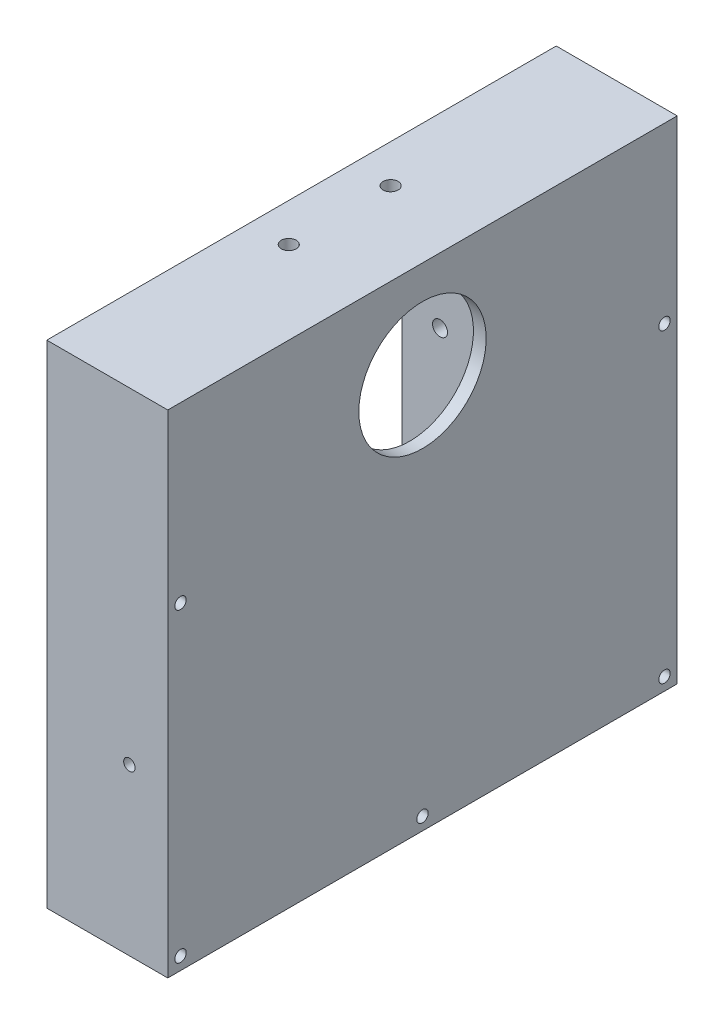
SolidWorks part; units mm, degrees
ref_plane "정면" through (0, 0, 0) normal (0, 0, 1) x (1, 0, 0)
ref_plane "윗면" through (0, 0, 0) normal (0, 1, 0) x (1, 0, 0)
ref_plane "우측면" through (0, 0, 0) normal (1, 0, 0) x (0, 0, -1)
ref_plane "평면1" through (0, 0, 0) normal (-1, 0, 0) x (0, -1, 0)
sketch "스케치1" plane through (0, 0, 0) normal (-1, 0, 0) x (0, -1, 0)
  line L0 (26.75, -54.25) -> (26.75, 25.75)
  line L1 (26.75, 25.75) -> (-73.25, 25.75)
  line L2 (-73.25, 25.75) -> (-73.25, -54.25)
  line L3 (-73.25, -54.25) -> (26.75, -54.25)
extrude "보스-돌출1" add sketch "스케치1" against normal blind 19
sketch "스케치2" plane through (0, 0, 0) normal (-1, 0, 0) x (0, 0, 1)
  line L0 (-50.25, 69.25) -> (-50.25, -22.75)
  line L1 (-50.25, -22.75) -> (21.75, -22.75)
  line L2 (21.75, -22.75) -> (21.75, 69.25)
  line L3 (21.75, 69.25) -> (-50.25, 69.25)
extrude "컷-돌출1" cut sketch "스케치2" against normal blind 17
sketch "스케치3" plane through (17, 0, 0) normal (-1, 0, 0) x (0, 0, 1)
  line L0 (4, 50.5) -> (4, -4)
  line L1 (4, -4) -> (-32.5, -4)
  line L2 (-32.5, -4) -> (-32.5, 50.5)
  line L3 (-32.5, 50.5) -> (4, 50.5)
extrude "보스-돌출2" add sketch "스케치3" along normal blind 17
sketch "스케치4" plane through (0, 0, 0) normal (-1, 0, 0) x (0, 0, 1)
  line L0 (1.5, 48) -> (-30, 48)
  line L1 (-30, 48) -> (-30, -1.5)
  line L2 (-30, -1.5) -> (1.5, -1.5)
  line L3 (1.5, -1.5) -> (1.5, 48)
extrude "컷-돌출2" cut sketch "스케치4" against normal blind 17
hole_wizard "Ø20.0 (20) 지름 구멍1" positions "스케치6" profile "스케치5" hole size "Ø20.0" standard "Ansi Metric"
sketch "스케치6" plane through (17, 0, 0) normal (-1, 0, 0) x (0, 0, 1)
  point P0 (-14.25, 35.25)
sketch "스케치5" plane through (17, 35.25, -14.25) normal (0, 1, 0) x (0, 0, 1)
  line L0 (0, 0) -> (0, 2)
  line L1 (0, 2) -> (10, 2)
  line L2 (10, 2) -> (10, 0)
  line L5 (10, 0) -> (0, 0)
  line L11 (0, -6.35) -> (0, 107.95) construction
  dimension "관통 구멍 지름" = 20
  dimension "관통 구멍 깊이" = 2
hole_wizard "Ø1.8 (1.8) 지름 구멍1" positions "스케치8" profile "스케치7" hole size "Ø1.8" standard "Ansi Metric" end condition through all
sketch "스케치8" plane through (0, 0, 0) normal (-1, 0, 0) x (0, 0, 1)
  point P0 (-52.25, 71.25)
  point P1 (-14.25, 71.25)
  point P2 (23.75, 71.25)
  point P3 (23.75, -24.75)
  point P4 (-14.25, -24.75)
  point P5 (-52.25, -24.75)
  point P6 (-52.25, 23.25)
  point P7 (23.75, 23.25)
sketch "스케치7" plane through (0, 71.25, -52.25) normal (0, 1, 0) x (0, 0, 1)
  line L0 (0, 0) -> (0, 19)
  line L1 (0, 19) -> (0.9, 19)
  line L2 (0.9, 19) -> (0.9, 0)
  line L5 (0.9, 0) -> (0, 0)
  line L11 (0, -6.35) -> (0, 107.95) construction
  dimension "관통 구멍 지름" = 1.8
  dimension "관통 구멍 깊이" = 19
hole_wizard "Ø1.8 (1.8) 지름 구멍2" positions "스케치10" profile "스케치9" hole size "Ø1.8" standard "Ansi Metric"
sketch "스케치10" plane through (0, 0, -50.25) normal (0, 0, 1) x (1, 0, 0)
  point P0 (12.975, -0.75)
  point P1 (12.975, 47.25)
sketch "스케치9" plane through (12.975, -0.75, -50.25) normal (1, 0, 0) x (0, -1, 0)
  line L0 (0, 0) -> (0, 4)
  line L1 (0, 4) -> (0.9, 4)
  line L2 (0.9, 4) -> (0.9, 0)
  line L5 (0.9, 0) -> (0, 0)
  line L11 (0, -6.35) -> (0, 107.95) construction
  dimension "관통 구멍 지름" = 1.8
  dimension "관통 구멍 깊이" = 4
hole_wizard "Ø1.8 (1.8) 지름 구멍3" positions "스케치12" profile "스케치11" hole size "Ø1.8" standard "Ansi Metric"
sketch "스케치12" plane through (0, 0, 21.75) normal (0, 0, -1) x (-1, 0, 0)
  point P0 (-12.975, -0.75)
  point P1 (-12.975, 47.25)
sketch "스케치11" plane through (12.975, -0.75, 21.75) normal (1, 0, 0) x (0, 1, 0)
  line L0 (0, 0) -> (0, 4)
  line L1 (0, 4) -> (0.9, 4)
  line L2 (0.9, 4) -> (0.9, 0)
  line L5 (0.9, 0) -> (0, 0)
  line L11 (0, -6.35) -> (0, 107.95) construction
  dimension "관통 구멍 지름" = 1.8
  dimension "관통 구멍 깊이" = 4
hole_wizard "Ø2.35 (2.35) 지름 구멍1" positions "스케치14" profile "스케치13" hole size "Ø2.35" standard "Ansi Metric" end condition up to next
sketch "스케치14" plane through (0, -1.5, 0) normal (0, 1, 0) x (1, 0, 0)
  point P0 (6, 6.25)
  point P1 (6, 22.25)
sketch "스케치13" plane through (6, -1.5, -6.25) normal (1, 0, 0) x (0, 0, 1)
  line L0 (0, 0) -> (0, 2.5)
  line L1 (0, 2.5) -> (1.175, 2.5)
  line L2 (1.175, 2.5) -> (1.175, 0)
  line L5 (1.175, 0) -> (0, 0)
  line L11 (0, -6.35) -> (0, 107.95) construction
  dimension "관통 구멍 지름" = 2.35
  dimension "관통 구멍 깊이" = 2.5
hole_wizard "Ø2.35 (2.35) 지름 구멍2" positions "스케치16" profile "스케치15" hole size "Ø2.35" standard "Ansi Metric" end condition up to next
sketch "스케치16" plane through (0, 0, -30) normal (0, 0, 1) x (1, 0, 0)
  point P0 (6, 27.25)
  point P1 (6, 3.25)
sketch "스케치15" plane through (6, 27.25, -30) normal (1, 0, 0) x (0, -1, 0)
  line L0 (0, 0) -> (0, 2.5)
  line L1 (0, 2.5) -> (1.175, 2.5)
  line L2 (1.175, 2.5) -> (1.175, 0)
  line L5 (1.175, 0) -> (0, 0)
  line L11 (0, -6.35) -> (0, 107.95) construction
  dimension "관통 구멍 지름" = 2.35
  dimension "관통 구멍 깊이" = 2.5
hole_wizard "Ø2.35 (2.35) 지름 구멍3" positions "스케치18" profile "스케치17" hole size "Ø2.35" standard "Ansi Metric" end condition up to next
sketch "스케치18" plane through (0, 48, 0) normal (0, -1, 0) x (-1, 0, 0)
  point P0 (-6, 6.25)
  point P1 (-6, 22.25)
sketch "스케치17" plane through (6, 48, -6.25) normal (1, 0, 0) x (0, 0, -1)
  line L0 (0, 0) -> (0, 2.5)
  line L1 (0, 2.5) -> (1.175, 2.5)
  line L2 (1.175, 2.5) -> (1.175, 0)
  line L5 (1.175, 0) -> (0, 0)
  line L11 (0, -6.35) -> (0, 107.95) construction
  dimension "관통 구멍 지름" = 2.35
  dimension "관통 구멍 깊이" = 2.5
hole_wizard "Ø2.35 (2.35) 지름 구멍4" positions "스케치20" profile "스케치19" hole size "Ø2.35" standard "Ansi Metric" end condition up to next
sketch "스케치20" plane through (0, 0, 1.5) normal (0, 0, -1) x (-1, 0, 0)
  point P0 (-6, 27.25)
  point P1 (-6, 3.25)
sketch "스케치19" plane through (6, 27.25, 1.5) normal (1, 0, 0) x (0, 1, 0)
  line L0 (0, 0) -> (0, 2.5)
  line L1 (0, 2.5) -> (1.175, 2.5)
  line L2 (1.175, 2.5) -> (1.175, 0)
  line L5 (1.175, 0) -> (0, 0)
  line L11 (0, -6.35) -> (0, 107.95) construction
  dimension "관통 구멍 지름" = 2.35
  dimension "관통 구멍 깊이" = 2.5
sketch "스케치21" plane through (0, 73.25, 0) normal (0, 1, 0) x (1, 0, 0)
  line L0 (0, -25.75) -> (0, 54.25) construction
  line L1 (15, -4) -> (0, -4)
  line L2 (15, -4) -> (15, 32.5)
  line L3 (15, 32.5) -> (0, 32.5)
  line L4 (0, -4) -> (0, 32.5)
  line L5 (15, -4) -> (0, 32.5) construction
  line L6 (15, 32.5) -> (0, -4) construction
  line L7 (19, -25.75) -> (19, 54.25) construction
  line L9 (19, 54.25) -> (0, 54.25) construction
  line L10 (19, -25.75) -> (0, -25.75) construction
  point P0 (7.5, 14.25)
  point P7 (15, 14.25)
  dimension "D1" = 0
  dimension "D2" = 4
  dimension "D3" = 36.5
  dimension "D4" = 21.75
  dimension "D5" = 80
sketch "스케치22" plane through (0, -26.75, 0) normal (0, -1, 0) x (1, 0, 0)
  line L0 (0, -54.25) -> (0, 25.75) construction
  line L1 (0, 4) -> (13, 4)
  line L2 (0, 4) -> (0, -32.5)
  line L3 (0, -32.5) -> (13, -32.5)
  line L4 (13, 4) -> (13, -32.5)
  line L5 (0, 4) -> (13, -32.5) construction
  line L6 (0, -32.5) -> (13, 4) construction
  line L7 (19, -54.25) -> (19, 25.75) construction
  line L8 (19, -54.25) -> (0, -54.25) construction
  point P0 (6.5, -14.25)
  dimension "D1" = 36.5
  dimension "D2" = 0
  dimension "D3" = 6
  dimension "D4" = 21.75
extrude "컷-돌출5" cut sketch "스케치22" against normal blind 10
sketch "스케치23" plane through (0, 0, 0) normal (-1, 0, 0) x (0, 0, 1)
  line L0 (-54.25, 73.25) -> (-54.25, -26.75) construction
  line L1 (25.75, 73.25) -> (-54.25, 73.25)
  line L2 (25.75, 73.25) -> (25.75, 50.5)
  line L3 (25.75, 50.5) -> (-54.25, 50.5)
  line L4 (-54.25, 73.25) -> (-54.25, 50.5)
  line L5 (4, 50.5) -> (-32.5, 50.5) construction
  dimension "D1" = 0
extrude "컷-돌출6" cut sketch "스케치23" against normal up to surface (19 mm away) up to face at (19, 71.25, -51.35)
sketch "스케치24" plane through (0, 50.5, 0) normal (0, 1, 0) x (1, 0, 0)
  line L0 (17, 50.25) -> (0, 50.25) construction
  line L1 (17, -21.75) -> (0, -21.75)
  line L2 (17, -21.75) -> (17, -4)
  line L3 (17, -4) -> (0, -4)
  line L4 (0, -21.75) -> (0, -4)
  line L5 (17, 32.5) -> (0, 32.5)
  line L6 (17, 32.5) -> (17, 50.25)
  line L7 (17, 50.25) -> (0, 50.25)
  line L8 (0, 32.5) -> (0, 50.25)
extrude "보스-돌출3" add sketch "스케치24" against normal blind 4
sketch "스케치25" plane through (0, 0, 25.75) normal (0, 0, 1) x (1, 0, 0)
  circle A0 centre (12.975, 47.25) radius 0.9
  circle A1 centre (12.975, 47.25) radius 0.9 construction
  dimension "D1" = 0
extrude "보스-돌출4" add sketch "스케치25" against normal up to surface (4 mm away) up to face at (12.975, 0.15, 21.75)
sketch "스케치26" plane through (0, 0, -54.25) normal (0, 0, -1) x (-1, 0, 0)
  circle A0 centre (-12.975, 47.25) radius 0.9
extrude "보스-돌출5" add sketch "스케치26" against normal up to vertex
